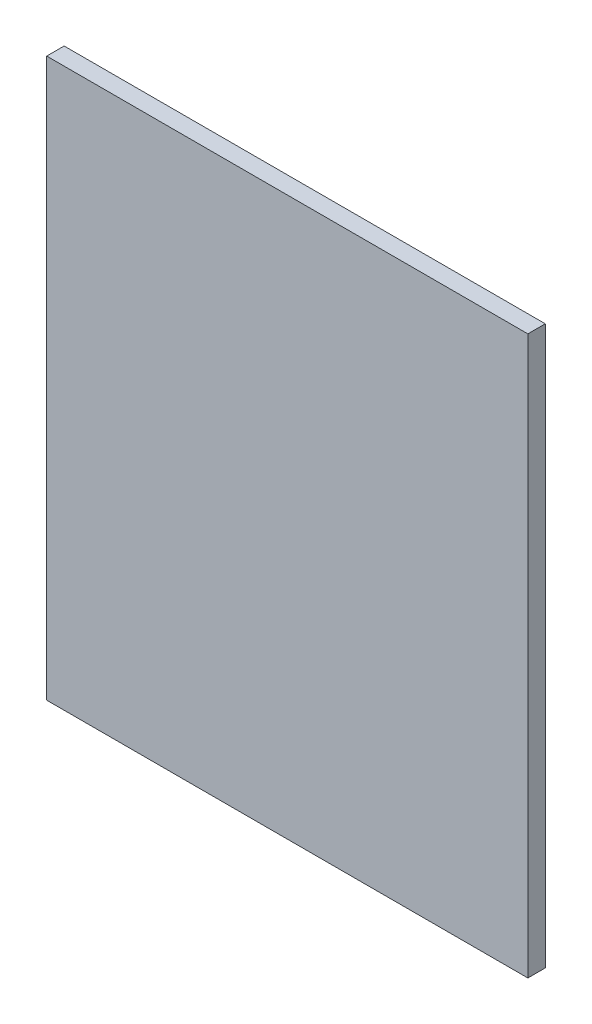
SolidWorks part; units mm, degrees
ref_plane "Front Plane" through (0, 0, 0) normal (0, 0, 1) x (1, 0, 0)
ref_plane "Top Plane" through (0, 0, 0) normal (0, 1, 0) x (1, 0, 0)
ref_plane "Right Plane" through (0, 0, 0) normal (1, 0, 0) x (0, 0, -1)
sketch "Sketch1" plane through (0, 0, 0) normal (0, 0, 1) x (1, 0, 0)
  line L1 (-43.815, 50.8) -> (43.815, 50.8)
  line L2 (-43.815, 50.8) -> (-43.815, -50.8)
  line L3 (-43.815, -50.8) -> (43.815, -50.8)
  line L4 (43.815, 50.8) -> (43.815, -50.8)
  dimension "D1" = 87.63
  dimension "D2" = 101.6
  dimension "D3" = 50.8
  dimension "D4" = 43.815
extrude "Boss-Extrude1" add sketch "Sketch1" along normal blind 3.175
equation "\"D3@Sketch1\"=\"D2@Sketch1\"/2"
equation "\"D4@Sketch1\"=\"D1@Sketch1\"/2"
